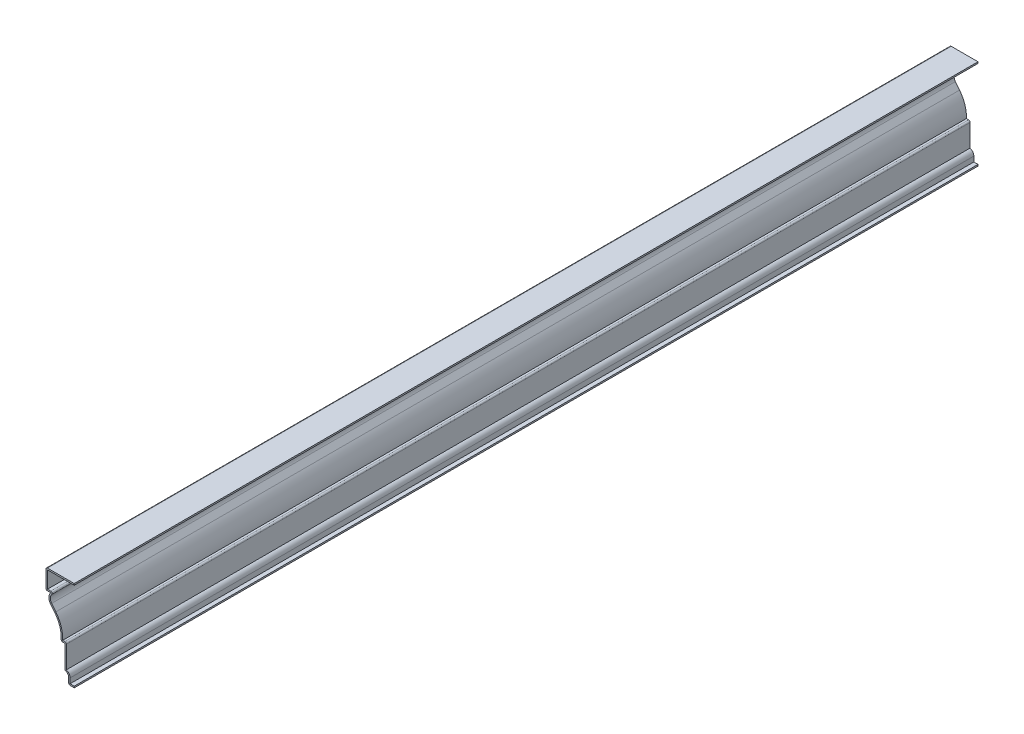
SolidWorks part; units mm, degrees
ref_plane "Front Plane" through (0, 0, 0) normal (0, 0, 1) x (1, 0, 0)
ref_plane "Top Plane" through (0, 0, 0) normal (0, 1, 0) x (1, 0, 0)
ref_plane "Right Plane" through (0, 0, 0) normal (1, 0, 0) x (0, 0, -1)
sketch "Sketch1" plane through (0, 0, 0) normal (0, 0, 1) x (1, 0, 0)
  line L0 (0, 0) -> (-4.7625, 0)
  line L1 (-4.7625, 0) -> (-4.7625, 5.5563)
  line L2 (-7.9375, 8.7313) -> (-7.9375, 28.575)
  line L3 (-7.9375, 28.575) -> (-11.1125, 28.575)
  line L4 (-16.5222, 46.946) -> (-20.049, 51.3711)
  line L5 (-19.8438, 59.5312) -> (-23.8125, 59.5313)
  line L6 (-23.8125, 59.5313) -> (-23.8125, 76.2)
  line L7 (-23.8125, 76.2) -> (0, 76.2)
  line L8 (0, 76.2) -> (0, 0) construction
  line L9 (-19.8437, 60.8013) -> (-22.5425, 60.8013)
  line L10 (-22.5425, 60.8013) -> (-22.5425, 74.93)
  line L11 (-22.5425, 74.93) -> (0, 74.93)
  line L13 (0, 76.2) -> (0, 74.93)
  line L14 (-19.8438, 60.8013) -> (-22.5425, 60.8013) construction
  line L15 (0, 1.27) -> (-3.4925, 1.27)
  line L16 (-3.4925, 1.27) -> (-3.4925, 5.5563)
  line L17 (-6.6675, 9.816) -> (-6.6675, 29.845)
  line L18 (-6.6675, 29.845) -> (-9.7454, 29.845)
  line L19 (-15.529, 47.7376) -> (-19.0559, 52.1626)
  line L20 (0, 1.27) -> (0, 0)
  line L21 (-15.4555, 60.8013) -> (-22.5425, 60.8013) construction
  line L22 (-15.529, 47.7376) -> (-19.0559, 52.1626) construction
  line L27 (-15.4555, 59.5312) -> (-17.9374, 59.5312) construction
  line L28 (-17.9374, 59.5312) -> (-17.9374, 59.5312) construction
  line L29 (-17.9374, 59.5312) -> (-17.9374, 59.5312) construction
  line L30 (-17.9374, 59.5312) -> (-17.9374, 59.5312) construction
  line L31 (-17.9374, 59.5312) -> (-17.9374, 59.5312) construction
  line L32 (-17.9374, 59.5312) -> (-17.9374, 59.5312) construction
  line L33 (-17.9374, 59.5312) -> (-17.9374, 59.5312) construction
  arc A0 (-4.7625, 5.5563) -> (-7.9375, 8.7313) centre (-7.9375, 5.5563) ccw
  arc A1 (-11.1125, 28.575) -> (-16.5222, 46.946) centre (-36.3852, 31.115) ccw
  arc A2 (-20.049, 51.3711) -> (-19.8438, 59.5312) centre (-15.0833, 55.3288) cw
  arc A3 (-3.4925, 5.5563) -> (-6.6675, 9.816) centre (-7.9375, 5.5563) ccw
  arc A4 (-9.7454, 29.845) -> (-15.529, 47.7376) centre (-36.3852, 31.115) ccw
  arc A5 (-19.0559, 52.1626) -> (-18.8917, 58.6908) centre (-15.0833, 55.3288) cw
  arc A6 (-19.0559, 52.1626) -> (-17.9374, 59.5312) centre (-15.0833, 55.3288) cw construction
  arc A7 (-19.0559, 52.1626) -> (-18.8917, 58.6908) centre (-15.0833, 55.3288) cw construction
  arc A8 (-19.8437, 60.8013) -> (-18.8917, 58.6908) centre (-19.8437, 59.5312) cw
  point P19 (-19.8438, 60.8013)
  point P20 (0, 74.93)
  point P21 (-21.4312, 55.4885)
  point P22 (0, 1.27)
  point P23 (-18.3348, 51.3711)
  point P24 (0, 0)
  dimension "D8" = 3.175
  dimension "D11" = 25.4
  dimension "D12" = 6.35
  dimension "D17" = 1.27
  dimension "D1" = 76.2
  dimension "D2" = 23.8125
  dimension "D3" = 16.6687
  dimension "D4" = 30.9562
  dimension "D5" = 19.8438
  dimension "D6" = 4.7625
  dimension "D7" = 3.175
  dimension "D9" = 2.54
  dimension "D10" = 2.3813
  dimension "D13" = 3.9688
  dimension "D14" = 1.27
  dimension "D15" = 1.27
  dimension "D16" = 1.27
extrude "Boss-Extrude2" add sketch "Sketch1" against normal blind 762 contours L10 L11 L13 L7 L6 L5 A2 L4 A1 L3 L2 A0 L1 L0 L20 L15 L16 A3 L17 L18 A4 L19 A5 A8 L9
fillet "Fillet2" radius 1.27 6 edges at (-4.7625, 0, -381) (-7.9375, 8.7313, -381) (-6.6675, 29.845, -381) (-11.1125, 28.575, -381) (-23.8125, 59.5313, -381) (-23.8125, 76.2, -381)
